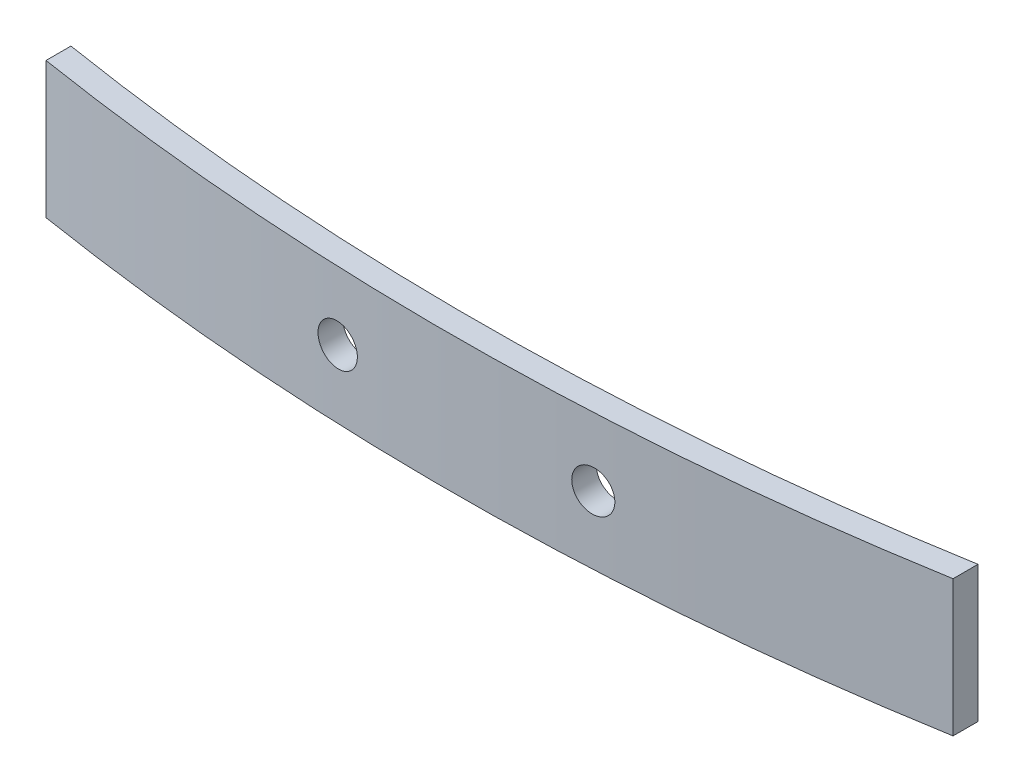
SolidWorks part; units mm, degrees
ref_plane "Front Plane" through (0, 0, 0) normal (0, 0, 1) x (1, 0, 0)
ref_plane "Top Plane" through (0, 0, 0) normal (0, 1, 0) x (1, 0, 0)
ref_plane "Right Plane" through (0, 0, 0) normal (1, 0, 0) x (0, 0, -1)
sketch "Sketch1" plane through (0, 0, 0) normal (0, 1, 0) x (1, 0, 0)
  line L0 (-35, 4.1426) -> (35, 4.5206) construction
  line L3 (27.5, 11.7241) -> (27.5, -8.9893) construction
  line L4 (-27.5, -8.9719) -> (-27.5, 18.3807) construction
  line L5 (27.5, -0.2767) -> (27.5, -1.7985)
  line L6 (-27.5, -0.5651) -> (-27.5, -2.0843)
  arc A5 (-27.5, -0.5651) -> (27.5, -0.2767) centre (-0.865, 164.5106) ccw
  arc A6 (-27.5, -2.0843) -> (27.5, -1.7985) centre (-0.865, 164.5106) ccw
  arc A8 (-35.4132, 0.908) -> (35.4342, 1.2875) centre (-0.865, 164.5106) ccw construction
  arc A9 (-35.7232, -0.5597) -> (35.7598, -0.1767) centre (-0.865, 164.5106) ccw construction
  point P4 (-35, 4.1426)
  point P5 (-35, 2.8648)
  point P7 (38.108, 5.4708)
  point P8 (35, 4.5206)
  point P10 (-0.865, 164.5106)
  point P11 (35, 3.2398)
  point P18 (-31.892, 5.0928)
  dimension "D2" = 1.5
  dimension "D3" = 70
  dimension "D4" = 35
  dimension "D6" = 27.5
  dimension "D5" = 55
extrude "Boss-Extrude1" add sketch "Sketch1" along normal blind 8.3
sketch "Sketch2" plane through (0, 0, 0) normal (0, 0, 1) x (1, 0, 0)
  line L0 (0, 8.3) -> (0, 0) construction
  line L1 (27.5, 8.3) -> (-27.5, 8.3) construction
  line L2 (-27.5, 4.15) -> (27.5, 4.15) construction
  line L3 (-27.5, 8.3) -> (-27.5, 0) construction
  line L4 (27.5, 8.3) -> (27.5, 0) construction
  circle A0 centre (-7.75, 4.15) radius 1.25
  circle A1 centre (7.75, 4.15) radius 1.25
  point P15 (0, 0)
  dimension "D2" = 2.5
  dimension "D3" = 2.5
  dimension "D1" = 15.5
  dimension "D4" = 7.75
extrude "Cut-Extrude1" cut sketch "Sketch2" against normal through all both and the other way through all
